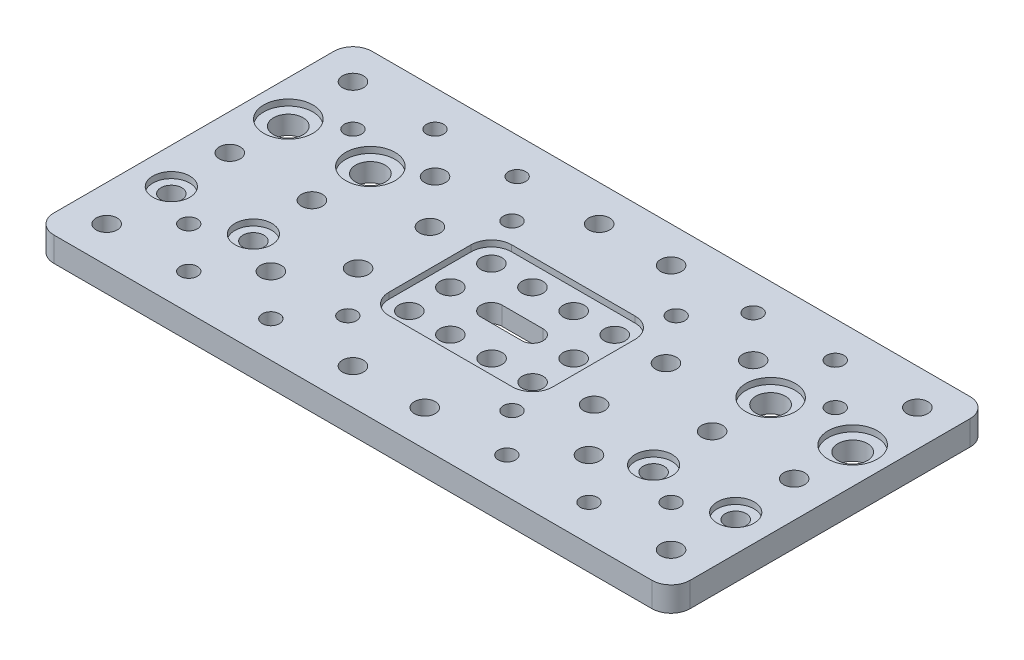
SolidWorks part; units mm, degrees
material "6061-T6 (SS)"
ref_plane "Front Plane" through (0, 0, 0) normal (0, 0, 1) x (1, 0, 0)
ref_plane "Top Plane" through (0, 0, 0) normal (0, 1, 0) x (1, 0, 0)
ref_plane "Right Plane" through (0, 0, 0) normal (1, 0, 0) x (0, 0, -1)
sketch "Sketch1" plane through (0, 0, 0) normal (0, 1, 0) x (1, 0, 0)
  line L1 (4.64, 0) -> (150.38, 0)
  line L2 (0, 4.64) -> (0, 72.88)
  line L3 (4.64, 77.52) -> (150.38, 77.52)
  line L4 (155.02, 4.64) -> (155.02, 72.88)
  arc A0 (150.38, 0) -> (155.02, 4.64) centre (150.38, 4.64) ccw
  arc A1 (150.38, 77.52) -> (155.02, 72.88) centre (150.38, 72.88) cw
  arc A2 (0, 72.88) -> (4.64, 77.52) centre (4.64, 72.88) cw
  arc A3 (4.64, 0) -> (0, 4.64) centre (4.64, 4.64) cw
  point P9 (155.02, 77.52)
  point P12 (0, 77.52)
  point P15 (0, 0)
  dimension "D3" = 4.64
  dimension "D1" = 77.52
  dimension "D2" = 155.02
extrude "Boss-Extrude1" add sketch "Sketch1" along normal blind 6
hole_wizard "Ø5.1 (5.1) Diameter Hole1" positions "Sketch3" profile "Sketch2" hole size "Ø5.1" standard "ANSI Metric" end condition through all
sketch "Sketch3" plane through (0, 6, 0) normal (0, 1, 0) x (1, 0, 0)
  line L0 (0, 38.76) -> (77.51, 38.76) construction
  line L1 (0, 72.88) -> (0, 4.64) construction
  line L2 (77.51, 38.76) -> (77.51, 77.52) construction
  line L3 (150.38, 77.52) -> (4.64, 77.52) construction
  point P0 (8.755, 68.76)
  point P2 (8.755, 38.76)
  point P4 (28.755, 38.76)
  point P6 (38.755, 58.76)
  point P8 (48.755, 47.515)
  point P10 (68.755, 68.76)
  point P12 (62.485, 48.76)
  point P14 (72.485, 48.76)
  point P16 (62.485, 38.76)
  point P36 (92.535, 38.76)
  point P37 (82.535, 48.76)
  point P38 (92.535, 48.76)
  point P39 (86.265, 68.76)
  point P40 (106.265, 47.515)
  point P41 (116.265, 58.76)
  point P42 (126.265, 38.76)
  point P43 (146.265, 38.76)
  point P44 (146.265, 68.76)
  point P47 (146.265, 8.76)
  point P48 (116.265, 18.76)
  point P49 (106.265, 30.005)
  point P50 (92.535, 28.76)
  point P51 (82.535, 28.76)
  point P52 (86.265, 8.76)
  point P53 (68.755, 8.76)
  point P54 (72.485, 28.76)
  point P55 (62.485, 28.76)
  point P56 (48.755, 30.005)
  point P57 (38.755, 18.76)
  point P58 (8.755, 8.76)
  dimension "D1" = 10
  dimension "D2" = 10
  dimension "D3" = 17.51
  dimension "D4" = 30
  dimension "D5" = 30
  dimension "D6" = 20
  dimension "D7" = 10.05
  dimension "D8" = 17.51
  dimension "D9" = 60
  dimension "D10" = 20
  dimension "D11" = 10
sketch "Sketch2" plane through (8.755, 6, -68.76) normal (1, 0, 0) x (0, 0, 1)
  line L0 (0, 0) -> (0, 6)
  line L1 (0, 6) -> (2.55, 6)
  line L2 (2.55, 6) -> (2.55, 0)
  line L5 (2.55, 0) -> (0, 0)
  line L11 (0, -6.35) -> (0, 107.95) construction
  dimension "Thru Hole Dia." = 5.1
  dimension "Thru Hole Depth" = 6
hole_wizard "M5x0.8 Tapped Hole1" positions "Sketch5" profile "Sketch4" tap size "M5x0.8" standard "ANSI Metric" end condition through all
sketch "Sketch5" plane through (0, 6, 0) normal (0, 1, 0) x (1, 0, 0)
  line L0 (0, 38.76) -> (77.51, 38.76) construction
  line L1 (0, 72.88) -> (0, 4.64) construction
  line L2 (77.51, 38.76) -> (77.51, 77.52) construction
  line L3 (150.38, 77.52) -> (4.64, 77.52) construction
  circle A0 centre (8.755, 68.76) radius 2.55 construction
  point P0 (18.75, 58.76)
  point P2 (28.755, 68.76)
  point P4 (48.755, 68.76)
  point P6 (57.51, 58.76)
  point P23 (48.755, 8.76)
  point P24 (57.51, 18.76)
  point P25 (18.75, 18.76)
  point P26 (28.755, 8.76)
  point P28 (106.265, 68.76)
  point P29 (97.51, 58.76)
  point P30 (97.51, 18.76)
  point P31 (106.265, 8.76)
  point P32 (126.265, 8.76)
  point P33 (136.27, 18.76)
  point P34 (126.265, 68.76)
  point P35 (136.27, 58.76)
  dimension "D5" = 20
  dimension "D1" = 20
  dimension "D2" = 40
  dimension "D3" = 60
  dimension "D4" = 40
  dimension "D6" = 38.76
sketch "Sketch4" plane through (18.75, 6, -58.76) normal (1, 0, 0) x (0, 0, 1)
  line L0 (0, 0) -> (0, 6)
  line L1 (0, 6) -> (2.1, 6)
  line L2 (2.1, 6) -> (2.1, 0)
  line L5 (2.1, 0) -> (0, 0)
  line L11 (0, -6.35) -> (0, 107.95) construction
  dimension "Thread Major Dia." = 4.2
  dimension "Thru Tap Drill Depth" = 6
sketch "Sketch6" plane through (0, 6, 0) normal (0, 1, 0) x (1, 0, 0)
  line L0 (77.51, 77.52) -> (77.51, 95.8918) construction
  line L1 (150.38, 77.52) -> (4.64, 77.52) construction
  line L2 (0, 38.76) -> (-8.4214, 38.76) construction
  line L3 (0, 72.88) -> (0, 4.64) construction
  line L4 (8.755, 68.76) -> (8.755, 53.01) construction
  circle A0 centre (8.755, 53.01) radius 3.6
  circle A1 centre (28.755, 53.01) radius 3.6
  circle A2 centre (8.755, 24.51) radius 2.55
  circle A3 centre (28.755, 24.51) radius 2.55
  circle A4 centre (126.265, 24.51) radius 2.55
  circle A5 centre (146.265, 24.51) radius 2.55
  circle A6 centre (126.265, 53.01) radius 3.6
  circle A7 centre (146.265, 53.01) radius 3.6
  dimension "D1" = 7.2
  dimension "D2" = 5.1
  dimension "D3" = 28.5
  dimension "D4" = 20
extrude "Cut-Extrude1" cut sketch "Sketch6" against normal through all
sketch "Sketch7" plane through (0, 6, 0) normal (0, 1, 0) x (1, 0, 0)
  line L0 (77.51, 77.52) -> (77.51, 38.76) construction
  line L1 (150.38, 77.52) -> (4.64, 77.52) construction
  line L2 (57.535, 23.81) -> (97.485, 53.71) construction
  line L3 (62.475, 53.71) -> (92.545, 53.71)
  line L4 (57.535, 48.77) -> (57.535, 28.75)
  line L5 (62.475, 23.81) -> (92.545, 23.81)
  line L6 (97.485, 48.77) -> (97.485, 28.75)
  line L7 (77.51, 38.76) -> (155.02, 38.76) construction
  line L8 (155.02, 4.64) -> (155.02, 72.88) construction
  circle A0 centre (8.755, 53.01) radius 6
  circle A1 centre (28.755, 53.01) radius 6
  circle A2 centre (8.755, 24.51) radius 4.5
  circle A3 centre (28.755, 24.51) radius 4.5
  circle A4 centre (126.265, 24.51) radius 4.5
  circle A5 centre (146.265, 24.51) radius 4.5
  circle A6 centre (126.265, 53.01) radius 6
  circle A7 centre (146.265, 53.01) radius 6
  arc A8 (92.545, 53.71) -> (97.485, 48.77) centre (92.545, 48.77) cw
  arc A9 (62.475, 53.71) -> (57.535, 48.77) centre (62.475, 48.77) ccw
  arc A10 (57.535, 28.75) -> (62.475, 23.81) centre (62.475, 28.75) ccw
  arc A11 (92.545, 23.81) -> (97.485, 28.75) centre (92.545, 28.75) ccw
  point P28 (77.51, 38.76)
  dimension "D1" = 12
  dimension "D2" = 9
  dimension "D5" = 4.94
  dimension "D3" = 39.95
  dimension "D4" = 29.9
extrude "Cut-Extrude2" cut sketch "Sketch7" against normal blind 1.5
sketch "Sketch8" plane through (0, 4.5, 0) normal (0, 1, 0) x (1, 0, 0)
  line L0 (72.485, 38.76) -> (82.535, 38.76) construction
  line L1 (72.485, 41.31) -> (82.535, 41.31)
  line L2 (72.485, 36.21) -> (82.535, 36.21)
  line L3 (77.51, 38.76) -> (77.51, 53.71) construction
  line L4 (92.545, 53.71) -> (62.475, 53.71) construction
  line L5 (72.485, 38.76) -> (57.535, 38.76) construction
  line L6 (57.535, 48.77) -> (57.535, 28.75) construction
  arc A0 (72.485, 41.31) -> (72.485, 36.21) centre (72.485, 38.76) ccw
  arc A1 (82.535, 36.21) -> (82.535, 41.31) centre (82.535, 38.76) ccw
  point P2 (77.51, 38.76)
  dimension "D1" = 10.05
  dimension "D2" = 5.1
extrude "Cut-Extrude3" cut sketch "Sketch8" against normal through all
